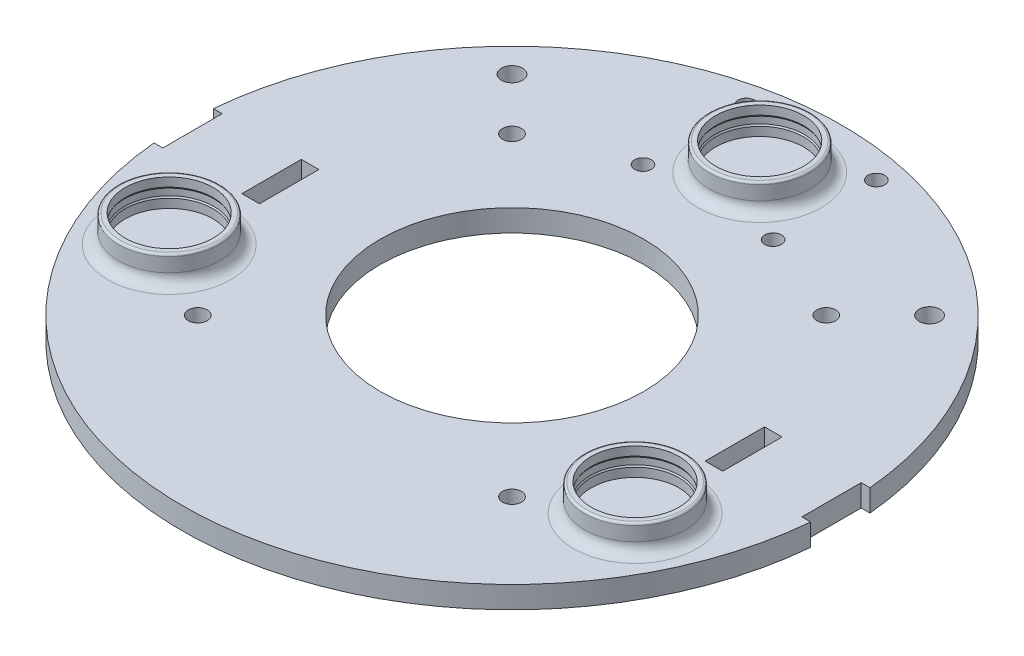
SolidWorks part; units mm, degrees
ref_plane "Front Plane" through (0, 0, 0) normal (0, 0, 1) x (1, 0, 0)
ref_plane "Top Plane" through (0, 0, 0) normal (0, 1, 0) x (1, 0, 0)
ref_plane "Right Plane" through (0, 0, 0) normal (1, 0, 0) x (0, 0, -1)
sketch "Sketch1" plane through (0, 0, 0) normal (0, 1, 0) x (1, 0, 0)
  line L0 (0, 75) -> (0, -75) construction
  line L1 (-75, 0) -> (75, 0) construction
  circle A0 centre (0, 0) radius 75
  dimension "D1" = 150
extrude "Base" add sketch "Sketch1" along normal blind 5
sketch "Sketch2" plane through (0, 5, 0) normal (0, 1, 0) x (1, 0, 0)
  line L0 (0, 75) -> (0, -75) construction
  line L1 (-75, 0) -> (75, 0) construction
  line L2 (74.6956, 6.75) -> (72.6956, 6.75)
  line L3 (72.6956, 6.75) -> (72.6956, -6.75)
  line L6 (54.6956, 6.75) -> (50.6956, 6.75)
  line L7 (54.6956, 6.75) -> (54.6956, -6.75)
  line L9 (50.6956, 6.75) -> (50.6956, -6.75)
  line L10 (74.6956, -6.75) -> (72.6956, -6.75)
  line L11 (54.6956, -6.75) -> (50.6956, -6.75)
  line L12 (-74.6956, -6.75) -> (-72.6956, -6.75)
  line L13 (-74.6956, 6.75) -> (-72.6956, 6.75)
  line L14 (-72.6956, 6.75) -> (-72.6956, -6.75)
  line L15 (-54.6956, 6.75) -> (-50.6956, 6.75)
  line L16 (-50.6956, 6.75) -> (-50.6956, -6.75)
  line L17 (-54.6956, -6.75) -> (-50.6956, -6.75)
  line L18 (-54.6956, 6.75) -> (-54.6956, -6.75)
  circle A0 centre (0, 0) radius 75 construction
  point P15 (73.6956, 6.75)
  point P16 (73.6956, -6.75)
  point P19 (72.6956, 0)
  point P20 (54.6956, 0)
  point P21 (50.6956, 0)
  circle M11 centre (0, 0) radius 75
  dimension "D1" = 6.75
  dimension "D2" = 2
  dimension "D3" = 18
  dimension "D4" = 6.75
  dimension "D5" = 4
extrude "Main Wheel Slots" cut sketch "Sketch2" against normal up to next contours L11 L7 L6 L9 | L10 L2 L3 M11 | L14 L13 L12 M11 | L16 L17 L18 L15
sketch "Sketch3" plane through (0, 5, 0) normal (0, 1, 0) x (1, 0, 0)
  line L0 (0, 75) -> (0, -75) construction
  line L1 (-72.6956, 0) -> (72.6956, 0) construction
  line L2 (-72.6956, 6.75) -> (-72.6956, -6.75) construction
  line L3 (72.6956, 6.75) -> (72.6956, -6.75) construction
  arc A0 (74.6956, 6.75) -> (-74.6956, 6.75) centre (0, 0) ccw construction
  arc A1 (-74.6956, -6.75) -> (74.6956, -6.75) centre (0, 0) ccw construction
  circle A2 centre (14.8, 68.1) radius 1.9
  circle A3 centre (14.8, 44.6) radius 1.9
  circle A4 centre (-14.8, 44.6) radius 1.9
  circle A5 centre (-14.8, 68.1) radius 1.9
  dimension "D1" = 3.8
  dimension "D3" = 5
  dimension "D4" = 3.8
  dimension "D2" = 14.8
  dimension "D5" = 14.8
  dimension "D6" = 23.5
extrude "3rd Wheel Holes" cut sketch "Sketch3" against normal up to next
sketch "Sketch6" plane through (0, 5, 0) normal (0, 1, 0) x (1, 0, 0)
  line L0 (0, 75) -> (0, -75) construction
  line L1 (-72.6956, 0) -> (72.6956, 0) construction
  line L2 (-72.6956, 6.75) -> (-72.6956, -6.75) construction
  line L3 (72.6956, 6.75) -> (72.6956, -6.75) construction
  line L4 (-75, 0) -> (75, 0) construction
  arc A0 (74.6956, 6.75) -> (-74.6956, 6.75) centre (0, 0) ccw construction
  arc A1 (-74.6956, -6.75) -> (74.6956, -6.75) centre (0, 0) ccw construction
  circle A2 centre (35.75, 35.75) radius 2.15
  circle A4 centre (-35.75, 35.75) radius 2.15
  circle A5 centre (-35.75, -35.75) radius 2.15
  circle A6 centre (35.75, -35.75) radius 2.15
  dimension "D1" = 4.3
  dimension "D2" = 35.75
  dimension "D3" = 0
  dimension "D4" = 35.75
extrude "Fan Screw Holes" cut sketch "Sketch6" against normal blind 6
sketch "Sketch7" plane through (0, 5, 0) normal (0, 1, 0) x (1, 0, 0)
  line L0 (-75, 0) -> (75, 0) construction
  circle A0 centre (0, 0) radius 30
  arc A1 (-74.6956, -6.75) -> (74.6956, -6.75) centre (0, 0) ccw construction
  point P3 (0, 0)
  point P4 (0, -15)
  dimension "D1" = 60
  dimension "D2" = 0
extrude "Fan Blade Hole" cut sketch "Sketch7" against normal up to next
ref_plane "Plane1" through (0, 0, -56.35) normal (0, 0, 1) x (1, 0, 0)
sketch "Sketch10" plane through (0, 0, -56.35) normal (0, 0, 1) x (1, 0, 0)
  line L0 (0, 0) -> (0, 15) construction
  line L1 (0, 5) -> (0, 15) construction
  line L2 (74.6956, 5) -> (-74.6956, 5) construction
  line L4 (10, 5) -> (10, 7)
  line L5 (10, 7) -> (10.2, 7.3464)
  line L6 (10.2, 7.3464) -> (10.2, 8.8464)
  line L7 (10.2, 8.8464) -> (10, 9.1928)
  line L8 (10, 9.1928) -> (10, 11.1928)
  line L11 (10, 11.1928) -> (11.5, 11.1928)
  line L12 (11.5, 11.1928) -> (11.5, 5)
  line L13 (11.5, 5) -> (10, 5)
  dimension "D1" = 15
  dimension "D2" = 0
  dimension "D3" = 10
  dimension "D4" = 2
  dimension "D5" = 0.2
  dimension "D6" = 30
  dimension "D7" = 30
  dimension "D8" = 1.5
  dimension "D9" = 2
  dimension "D11" = 1.5
revolve "Top Peg Base" add sketch "Sketch10" angle 360 about L1
fillet "Top Peg Bottom Fillet" radius 2.5 1 edges at (0, 5, -44.85)
fillet "Top Peg Top Fillet" radius 0.5 1 edges at (0, 11.1928, -67.85)
ref_plane "Plane2" through (0, 0, 25) normal (0, 0, 1) x (1, 0, 0)
sketch "Sketch11" plane through (0, 0, 25) normal (0, 0, 1) x (1, 0, 0)
  line L0 (0, 5) -> (0, 15) construction
  line L1 (53, 5) -> (53, 15) construction
  line L2 (74.6956, 5) -> (-74.6956, 5) construction
  line L4 (63, 5) -> (63, 7)
  line L5 (63, 7) -> (63.2, 7.3464)
  line L6 (63.2, 7.3464) -> (63.2, 8.8464)
  line L7 (63.2, 8.8464) -> (63, 9.1928)
  line L8 (63, 9.1928) -> (63, 11.1928)
  line L11 (63, 11.1928) -> (64.5, 11.1928)
  line L12 (64.5, 11.1928) -> (64.5, 5)
  line L13 (64.5, 5) -> (63, 5)
  dimension "D2" = 53
  dimension "D3" = 10
  dimension "D4" = 2
  dimension "D5" = 0.2
  dimension "D6" = 30
  dimension "D7" = 30
  dimension "D8" = 1.5
  dimension "D9" = 2
  dimension "D10" = 10
  dimension "D11" = 1.5
revolve "Right Peg Base" add sketch "Sketch11" angle 360 about L1
fillet "Right Peg Bottom Fillet" radius 2.5 1 edges at (53, 5, 36.5)
fillet "Right Peg Top Fillet" radius 0.5 1 edges at (53, 11.1928, 13.5)
mirror "Left Peg" about plane through (0, 0, 0) normal (1, 0, 0) of "Right Peg Top Fillet", "Right Peg Bottom Fillet", "Right Peg Base"
sketch "Sketch12" plane through (0, 5, 0) normal (0, 1, 0) x (1, 0, 0)
  line L0 (0, 75) -> (0, -75) construction
  line L1 (-72.6956, 0) -> (72.6956, 0) construction
  line L2 (-72.6956, 6.75) -> (-72.6956, -6.75) construction
  line L3 (72.6956, 6.75) -> (72.6956, -6.75) construction
  arc A0 (74.6956, 6.75) -> (-74.6956, 6.75) centre (0, 0) ccw construction
  arc A1 (-74.6956, -6.75) -> (74.6956, -6.75) centre (0, 0) ccw construction
  circle A2 centre (47.5, 47.5) radius 2.4
  circle A3 centre (-47.5, 47.5) radius 2.4
  dimension "D1" = 4.8
  dimension "D3" = 47.5
  dimension "D2" = 47.5
extrude "Switch Holes" cut sketch "Sketch12" against normal up to next
